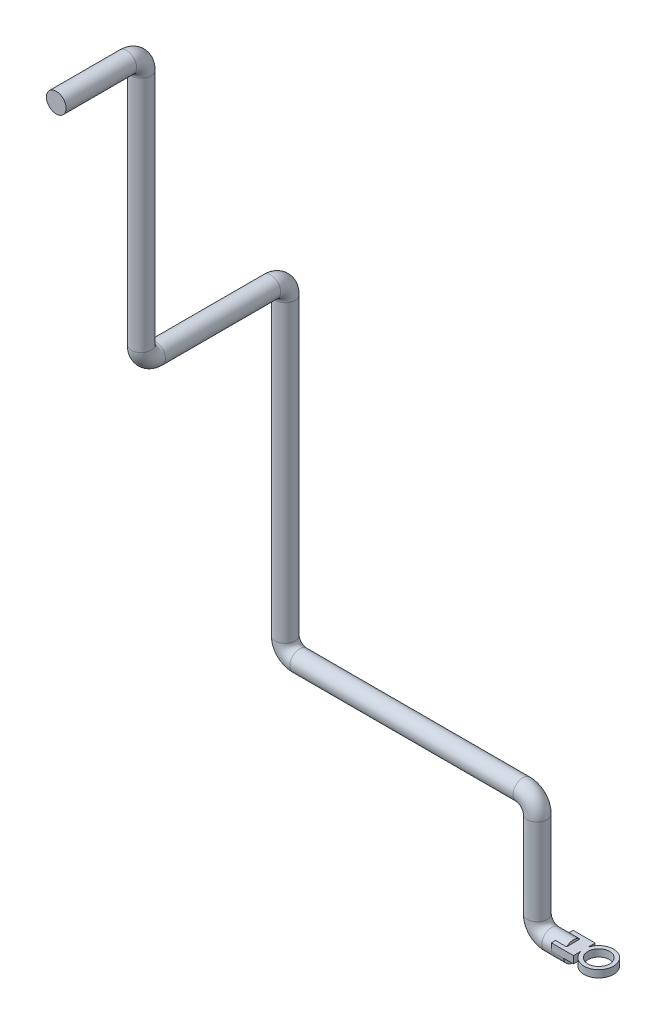
SolidWorks part; units mm, degrees
ref_plane "Alzado" through (0, 0, 0) normal (0, 0, 1) x (1, 0, 0)
ref_plane "Planta" through (0, 0, 0) normal (0, 1, 0) x (1, 0, 0)
ref_plane "Vista lateral" through (0, 0, 0) normal (1, 0, 0) x (0, 0, -1)
sketch3d "Croquis3D1"
  line L0 (0, 0, 0) -> (-30, 0, 0)
  line L1 (-50, 20, 0) -> (-50, 140, 0)
  line L2 (-70, 160, 0) -> (-380, 160, 0)
  line L3 (-400, 180, 0) -> (-400, 589.49, 0)
  line L4 (-400, 609.49, 20) -> (-400, 609.49, 180)
  line L5 (-400, 629.49, 200) -> (-400, 959.49, 200)
  line L6 (-400, 979.49, 220) -> (-400, 979.49, 318)
  arc A0 (-400, 959.49, 200) -> (-400, 979.49, 220) centre (-400, 959.49, 220) ccw
  arc A1 (-400, 609.49, 180) -> (-400, 629.49, 200) centre (-400, 629.49, 180) ccw
  arc A2 (-400, 589.49, 0) -> (-400, 609.49, 20) centre (-400, 589.49, 20) ccw
  arc A3 (-380, 160, 0) -> (-400, 180, 0) centre (-380, 180, 0) ccw
  arc A4 (-50, 140, 0) -> (-70, 160, 0) centre (-70, 140, 0) ccw
  arc A5 (-30, 0, 0) -> (-50, 20, 0) centre (-30, 20, 0) ccw
  point P12 (-400, 979.49, 200)
  point P13 (-380, 959.49, 220)
  point P16 (-400, 609.49, 200)
  point P17 (-420, 629.49, 180)
  point P20 (-400, 609.49, 0)
  point P21 (-380, 589.49, 20)
  point P24 (-400, 160, 0)
  point P25 (-380, 180, -20)
  point P28 (-50, 160, 0)
  point P29 (-70, 140, 20)
  point P32 (-50, 0, 0)
  point P33 (-30, 20, -20)
  dimension "D8" = 20
  dimension "D1" = 50
  dimension "D2" = 160
  dimension "D3" = 350
  dimension "D4" = 449.49
  dimension "D5" = 200
  dimension "D6" = 370
  dimension "D7" = 118
sketch "Croquis1" plane through (0, 0, 0) normal (1, 0, 0) x (0, 0, -1)
  circle A0 centre (0, 0) radius 13.7
  dimension "D1" = 27.4
sweep "Barrer1" add profiles "Croquis1" path "Croquis3D1"
sketch "Croquis2" plane through (0, 0, 0) normal (0, 1, 0) x (1, 0, 0)
  line L0 (0, 0) -> (35.3358, 0) construction
  line L2 (-15.3221, 15.0733) -> (15.3221, 15.0733)
  line L3 (-15.3221, 15.0733) -> (-15.3221, -15.0733)
  line L4 (-15.3221, -15.0733) -> (15.3221, -15.0733)
  line L5 (15.3221, 15.0733) -> (15.3221, -15.0733)
  line L6 (-15.3221, 15.0733) -> (15.3221, -15.0733) construction
  line L7 (-15.3221, -15.0733) -> (15.3221, 15.0733) construction
  circle A0 centre (35.3358, 0) radius 20.5158
  circle A1 centre (35.3358, 0) radius 15.0733
extrude "Saliente-Extruir1" add sketch "Croquis2" along normal blind 10 contours A0 L5 L2 L3 L4 | L5 A0 A1 | L5 A0
